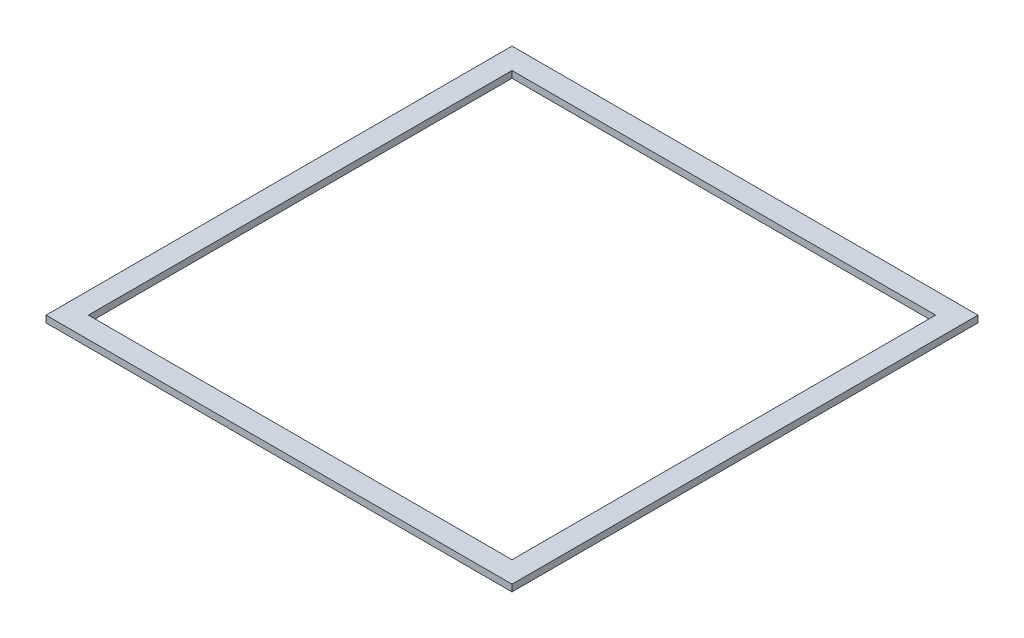
SolidWorks part; units mm, degrees
material "Rubber"
ref_plane "Front Plane" through (0, 0, 0) normal (0, 0, 1) x (1, 0, 0)
ref_plane "Top Plane" through (0, 0, 0) normal (0, 1, 0) x (1, 0, 0)
ref_plane "Right Plane" through (0, 0, 0) normal (1, 0, 0) x (0, 0, -1)
sketch "Sketch1" plane through (0, 0, 0) normal (0, 1, 0) x (1, 0, 0)
  line L0 (-50, 50) -> (50, 50)
  line L1 (-55, 55) -> (55, 55)
  line L2 (-55, 55) -> (-55, -55)
  line L3 (-55, -55) -> (55, -55)
  line L4 (55, 55) -> (55, -55)
  line L5 (-55, 55) -> (55, -55) construction
  line L6 (-55, -55) -> (55, 55) construction
  line L7 (50, 50) -> (50, -50)
  line L8 (-50, -50) -> (50, -50)
  line L9 (-50, 50) -> (-50, -50)
  point P0 (0, 0)
  dimension "D1" = 110
  dimension "D2" = 110
  dimension "D3" = 5
extrude "Boss-Extrude1" add sketch "Sketch1" along normal mid plane 1.5875
